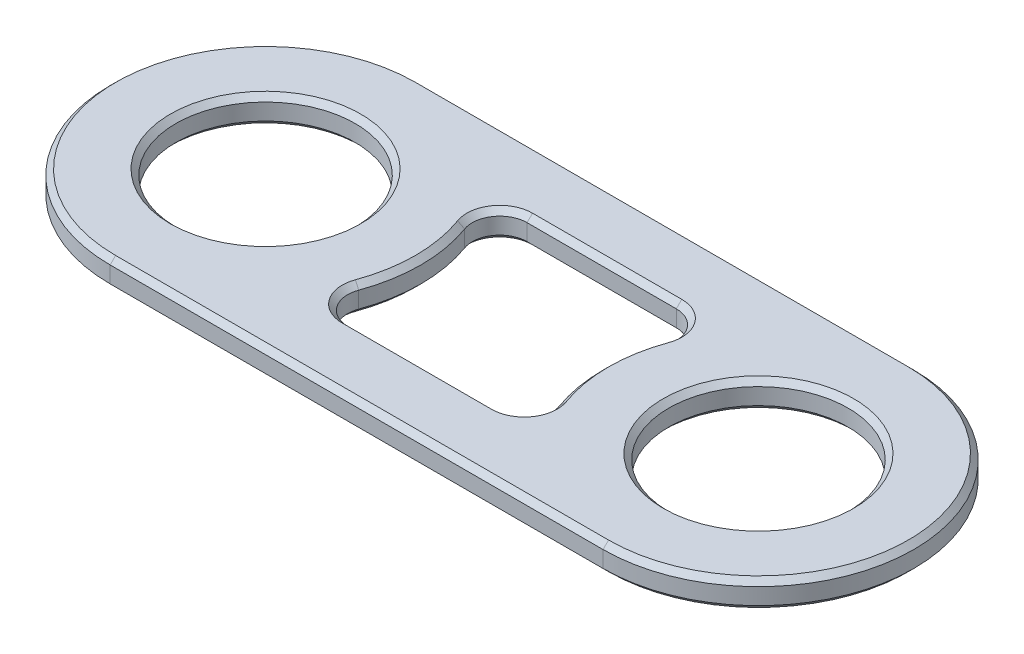
SolidWorks part; units mm, degrees
ref_plane "Front Plane" through (0, 0, 0) normal (0, 0, 1) x (1, 0, 0)
ref_plane "Top Plane" through (0, 0, 0) normal (0, 1, 0) x (1, 0, 0)
ref_plane "Right Plane" through (0, 0, 0) normal (1, 0, 0) x (0, 0, -1)
sketch "Sketch1" plane through (0, 0, 0) normal (0, 1, 0) x (1, 0, 0)
  line L0 (-9, 0) -> (9, 0) construction
  line L1 (-9, 5.675) -> (9, 5.675)
  line L2 (-9, -5.675) -> (9, -5.675)
  line L3 (-2.7247, 3.275) -> (2.7247, 3.275)
  line L4 (-2.7247, -3.275) -> (2.7247, -3.275)
  circle A0 centre (-9, 0) radius 3.275
  arc A1 (-9, 5.675) -> (-9, -5.675) centre (-9, 0) ccw
  arc A2 (9, -5.675) -> (9, 5.675) centre (9, 0) ccw
  circle A3 centre (9, 0) radius 3.275
  circle A4 centre (0, 0) radius 2.5 construction
  arc A5 (-3.6648, -1.9342) -> (-3.6648, 1.9342) centre (-9, 0) ccw
  arc A6 (3.6648, 1.9342) -> (3.6648, -1.9342) centre (9, 0) ccw
  arc A7 (2.7247, 3.275) -> (3.6648, 1.9342) centre (2.7247, 2.275) cw
  arc A8 (2.7247, -3.275) -> (3.6648, -1.9342) centre (2.7247, -2.275) ccw
  arc A9 (-2.7247, -3.275) -> (-3.6648, -1.9342) centre (-2.7247, -2.275) cw
  arc A10 (-2.7247, 3.275) -> (-3.6648, 1.9342) centre (-2.7247, 2.275) ccw
  point P6 (4.3653, 3.275)
  point P22 (-4.3653, -3.275)
  dimension "D1" = 5
  dimension "D2" = 6.55
  dimension "D3" = 2.4
  dimension "D5" = 1
  dimension "D4" = 18
extrude "Boss-Extrude1" add sketch "Sketch1" along normal blind 1
chamfer "Chamfer1" distance 0.2 angle 45 28 edges at (9, 0, 3.275) (3.325, 0, 0) (3.5434, 0, 2.8491) (0, 0, 3.275) (-3.5434, 0, 2.8491) (-3.325, 0, 0) (-3.5434, 0, -2.8491) (0, 0, -3.275) (3.5434, 0, -2.8491) (0, 0, 5.675) (14.675, 0, 0) (0, 0, -5.675) (-14.675, 0, 0) (-9, 0, 3.275) (9, 1, 3.275) (0, 1, -5.675) (14.675, 1, 0) (0, 1, 5.675) (-14.675, 1, 0) (-9, 1, 3.275) (-3.5434, 1, -2.8491) (-3.325, 1, 0) (-3.5434, 1, 2.8491) (0, 1, 3.275) (3.5434, 1, 2.8491) (3.325, 1, 0) (3.5434, 1, -2.8491) (0, 1, -3.275)
